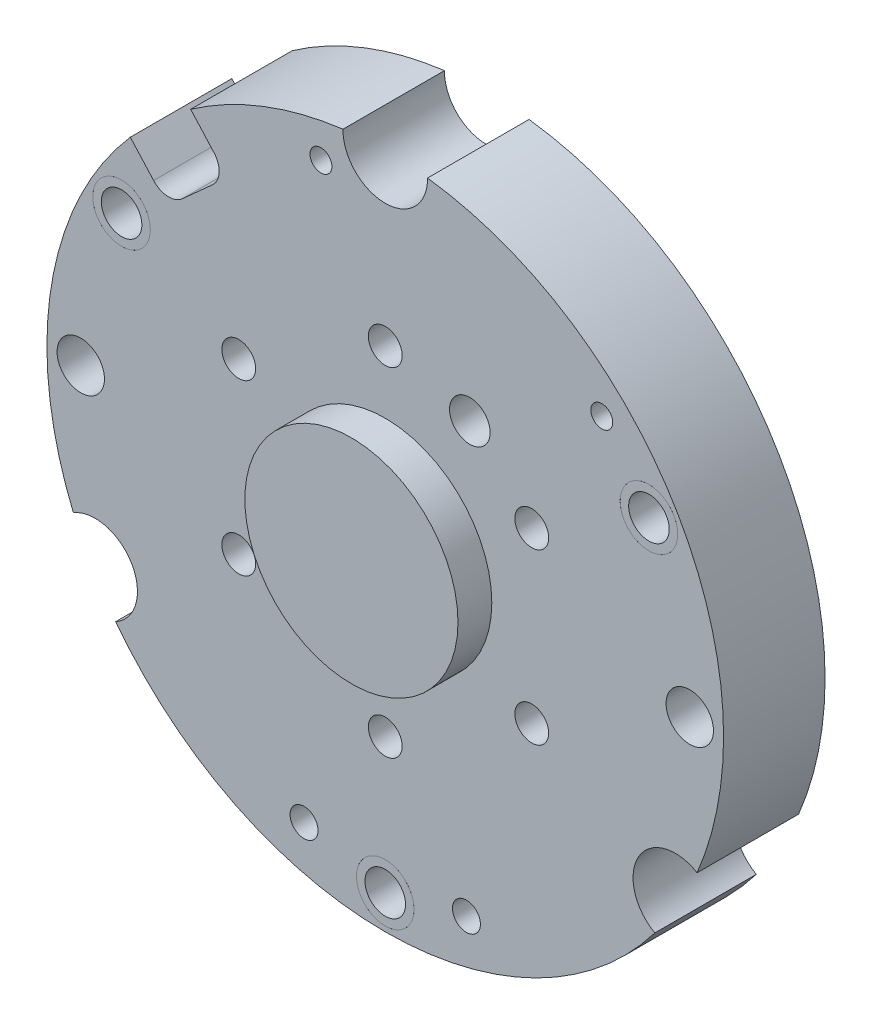
SolidWorks part; units mm, degrees
material "1060-H18"
ref_plane "Piano frontale" through (0, 0, 0) normal (0, 0, 1) x (1, 0, 0)
ref_plane "Piano superiore" through (0, 0, 0) normal (0, 1, 0) x (1, 0, 0)
ref_plane "Piano destro" through (0, 0, 0) normal (1, 0, 0) x (0, 0, -1)
sketch "Schizzo1" plane through (0, 0, 0) normal (0, 0, 1) x (1, 0, 0)
  line L3 (-34.2352, 29.0552) -> (-37.6736, 32.874)
  line L4 (-28.7559, 40.9035) -> (-25.3174, 37.0847)
  line L5 (-25.5395, 32.8479) -> (-29.9984, 28.8331)
  line L6 (-34.2352, 29.0552) -> (-37.6736, 32.874)
  line L7 (-28.7559, 40.9035) -> (-25.3174, 37.0847)
  line L8 (-25.5395, 32.8479) -> (-29.9984, 28.8331)
  arc A2 (32, 30.379) -> (32, 33.621) centre (32, 32) ccw
  arc A3 (32, 33.621) -> (32, 30.379) centre (32, 32) ccw
  arc A4 (32, 30.379) -> (32, 33.621) centre (32, 32) ccw
  arc A5 (32, 33.621) -> (32, 30.379) centre (32, 32) ccw
  arc A6 (-12, -44.067) -> (-12, -39.933) centre (-12, -42) ccw
  arc A7 (-12, -39.933) -> (-12, -44.067) centre (-12, -42) ccw
  arc A8 (-12, -44.067) -> (-12, -39.933) centre (-12, -42) ccw
  arc A9 (-34.2352, 29.0552) -> (-29.9984, 28.8331) centre (-32.0057, 31.0626) ccw
  arc A10 (-37.6736, 32.874) -> (-46.0866, -19.3913) centre (0, 0) ccw
  arc A11 (-39.8377, -30.2151) -> (-46.0866, -19.3913) centre (-42.87, -24.75) ccw
  arc A12 (-39.8377, -30.2151) -> (39.8377, -30.2151) centre (0, 0) ccw
  arc A13 (46.0866, -19.3913) -> (39.8377, -30.2151) centre (42.87, -24.75) ccw
  arc A14 (46.0866, -19.3913) -> (6.2491, 49.608) centre (0, 0) ccw
  arc A15 (-6.2491, 49.608) -> (6.2491, 49.608) centre (0, 49.5) ccw
  arc A16 (-6.2491, 49.608) -> (-28.7559, 40.9035) centre (0, 0) ccw
  arc A17 (-25.5395, 32.8479) -> (-25.3174, 37.0847) centre (-27.5469, 35.0773) ccw
  arc A18 (-34.2352, 29.0552) -> (-29.9984, 28.8331) centre (-32.0057, 31.0626) ccw
  arc A19 (-37.6736, 32.874) -> (-46.0866, -19.3913) centre (0, 0) ccw
  arc A20 (-39.8377, -30.2151) -> (-46.0866, -19.3913) centre (-42.87, -24.75) ccw
  arc A21 (-39.8377, -30.2151) -> (39.8377, -30.2151) centre (0, 0) ccw
  arc A22 (46.0866, -19.3913) -> (39.8377, -30.2151) centre (42.87, -24.75) ccw
  arc A23 (46.0866, -19.3913) -> (6.2491, 49.608) centre (0, 0) ccw
  arc A24 (-6.2491, 49.608) -> (6.2491, 49.608) centre (0, 49.5) ccw
  arc A25 (-6.2491, 49.608) -> (-28.7559, 40.9035) centre (0, 0) ccw
  arc A26 (-25.5395, 32.8479) -> (-25.3174, 37.0847) centre (-27.5469, 35.0773) ccw
  arc A27 (-12, -39.933) -> (-12, -44.067) centre (-12, -42) ccw
  arc A28 (12, -44.067) -> (12, -39.933) centre (12, -42) ccw
  arc A29 (12, -39.933) -> (12, -44.067) centre (12, -42) ccw
  arc A30 (12, -44.067) -> (12, -39.933) centre (12, -42) ccw
  arc A31 (12, -39.933) -> (12, -44.067) centre (12, -42) ccw
  arc A32 (-38.97, 26.75) -> (-38.97, 18.25) centre (-38.97, 22.5) ccw
  arc A33 (-38.97, 18.25) -> (-38.97, 26.75) centre (-38.97, 22.5) ccw
  arc A34 (-38.97, 26.75) -> (-38.97, 18.25) centre (-38.97, 22.5) ccw
  arc A35 (-38.97, 18.25) -> (-38.97, 26.75) centre (-38.97, 22.5) ccw
  arc A36 (38.97, 26.75) -> (38.97, 18.25) centre (38.97, 22.5) ccw
  arc A37 (38.97, 18.25) -> (38.97, 26.75) centre (38.97, 22.5) ccw
  arc A38 (38.97, 26.75) -> (38.97, 18.25) centre (38.97, 22.5) ccw
  arc A39 (38.97, 18.25) -> (38.97, 26.75) centre (38.97, 22.5) ccw
  arc A40 (0, -40.75) -> (0, -49.25) centre (0, -45) ccw
  arc A41 (0, -49.25) -> (0, -40.75) centre (0, -45) ccw
  arc A42 (0, -40.75) -> (0, -49.25) centre (0, -45) ccw
  arc A43 (0, -49.25) -> (0, -40.75) centre (0, -45) ccw
  arc A44 (-45, -3.5) -> (-45, 3.5) centre (-45, 0) ccw
  arc A45 (-45, 3.5) -> (-45, -3.5) centre (-45, 0) ccw
  arc A46 (-45, -3.5) -> (-45, 3.5) centre (-45, 0) ccw
  arc A47 (-45, 3.5) -> (-45, -3.5) centre (-45, 0) ccw
  arc A48 (45, -3.5) -> (45, 3.5) centre (45, 0) ccw
  arc A49 (45, 3.5) -> (45, -3.5) centre (45, 0) ccw
  arc A50 (45, -3.5) -> (45, 3.5) centre (45, 0) ccw
  arc A51 (45, 3.5) -> (45, -3.5) centre (45, 0) ccw
  arc A56 (-9.5, 42.379) -> (-9.5, 45.621) centre (-9.5, 44) ccw
  arc A57 (-9.5, 45.621) -> (-9.5, 42.379) centre (-9.5, 44) ccw
  arc A58 (-9.5, 42.379) -> (-9.5, 45.621) centre (-9.5, 44) ccw
  arc A59 (-9.5, 45.621) -> (-9.5, 42.379) centre (-9.5, 44) ccw
  dimension "D1" = 0
  dimension "D2" = 0
  dimension "D3" = 0
  dimension "D4" = 0
  dimension "D5" = 0
  dimension "D6" = 0
  dimension "D7" = 0
  dimension "D8" = 0
  dimension "D9" = 0
  dimension "D11" = 0
extrude "Estrusione-Estrusione1" add sketch "Schizzo1" along normal blind 15
sketch "Schizzo2" plane through (0, 0, 15) normal (0, 0, 1) x (1, 0, 0)
  arc A2 (-2.1651, -23.75) -> (2.1651, -26.25) centre (0, -25) ccw
  arc A3 (2.1651, -26.25) -> (-2.1651, -23.75) centre (0, -25) ccw
  arc A4 (-2.1651, -23.75) -> (2.1651, -26.25) centre (0, -25) ccw
  arc A5 (2.1651, -26.25) -> (-2.1651, -23.75) centre (0, -25) ccw
  arc A6 (19.4856, -11.25) -> (23.8157, -13.75) centre (21.6506, -12.5) ccw
  arc A7 (23.8157, -13.75) -> (19.4856, -11.25) centre (21.6506, -12.5) ccw
  arc A8 (19.4856, -11.25) -> (23.8157, -13.75) centre (21.6506, -12.5) ccw
  arc A9 (23.8157, -13.75) -> (19.4856, -11.25) centre (21.6506, -12.5) ccw
  arc A10 (19.4856, 13.75) -> (23.8157, 11.25) centre (21.6506, 12.5) ccw
  arc A11 (23.8157, 11.25) -> (19.4856, 13.75) centre (21.6506, 12.5) ccw
  arc A12 (19.4856, 13.75) -> (23.8157, 11.25) centre (21.6506, 12.5) ccw
  arc A13 (23.8157, 11.25) -> (19.4856, 13.75) centre (21.6506, 12.5) ccw
  arc A14 (9.9019, 23.1506) -> (15.0981, 20.1506) centre (12.5, 21.6506) ccw
  arc A15 (15.0981, 20.1506) -> (9.9019, 23.1506) centre (12.5, 21.6506) ccw
  arc A16 (9.9019, 23.1506) -> (15.0981, 20.1506) centre (12.5, 21.6506) ccw
  arc A17 (15.0981, 20.1506) -> (9.9019, 23.1506) centre (12.5, 21.6506) ccw
  arc A22 (-23.8157, -11.25) -> (-19.4856, -13.75) centre (-21.6506, -12.5) ccw
  arc A23 (-19.4856, -13.75) -> (-23.8157, -11.25) centre (-21.6506, -12.5) ccw
  arc A24 (-23.8157, -11.25) -> (-19.4856, -13.75) centre (-21.6506, -12.5) ccw
  arc A25 (-19.4856, -13.75) -> (-23.8157, -11.25) centre (-21.6506, -12.5) ccw
  arc A26 (-2.1651, 26.25) -> (2.1651, 23.75) centre (0, 25) ccw
  arc A27 (2.1651, 23.75) -> (-2.1651, 26.25) centre (0, 25) ccw
  arc A28 (-2.1651, 26.25) -> (2.1651, 23.75) centre (0, 25) ccw
  arc A29 (2.1651, 23.75) -> (-2.1651, 26.25) centre (0, 25) ccw
  arc A30 (-23.8157, 13.75) -> (-19.4856, 11.25) centre (-21.6506, 12.5) ccw
  arc A31 (-19.4856, 11.25) -> (-23.8157, 13.75) centre (-21.6506, 12.5) ccw
  arc A32 (-23.8157, 13.75) -> (-19.4856, 11.25) centre (-21.6506, 12.5) ccw
  arc A33 (-19.4856, 11.25) -> (-23.8157, 13.75) centre (-21.6506, 12.5) ccw
  dimension "D1" = 0
  dimension "D2" = 0
  dimension "D3" = 0
  dimension "D4" = 0
  dimension "D6" = 0
  dimension "D7" = 0
  dimension "D8" = 0
extrude "Taglio-Estrusione1" cut sketch "Schizzo2" against normal blind 15
sketch "Schizzo3" plane through (0, 0, 0) normal (0, 0, -1) x (-1, 0, 0)
  circle A74 centre (0, 25) radius 5.5
  circle A75 centre (0, 25) radius 5.5
  circle A85 centre (21.6506, 12.5) radius 5.5
  circle A86 centre (21.6506, -12.5) radius 5.5
  circle A87 centre (0, -25) radius 5.5
  circle A88 centre (-21.6506, -12.5) radius 5.5
  circle A89 centre (-21.6506, 12.5) radius 5.5
  dimension "D1" = 3
extrude "Taglio-Estrusione2" cut sketch "Schizzo3" against normal blind 5
sketch "Schizzo5" plane through (0, 0, 15) normal (0, 0, 1) x (1, 0, 0)
  arc A2 (13.6399, -7.875) -> (-13.6399, 7.875) centre (0, 0) ccw
  arc A3 (-13.6399, 7.875) -> (13.6399, -7.875) centre (0, 0) ccw
  arc A6 (13.6399, -7.875) -> (-13.6399, 7.875) centre (0, 0) ccw
  arc A7 (-13.6399, 7.875) -> (13.6399, -7.875) centre (0, 0) ccw
  dimension "D1" = 0
extrude "Estrusione-Estrusione2" add sketch "Schizzo5" along normal blind 5 separate body contours A7 A6
sketch "Schizzo6" plane through (0, 0, 0) normal (0, 0, -1) x (-1, 0, 0)
  circle A0 centre (0, 0) radius 35
extrude "Taglio-Estrusione3" cut sketch "Schizzo6" against normal blind 0.3
sketch "Schizzo7" plane through (0, 0, 0) normal (0, 0, -1) x (-1, 0, 0)
  circle A0 centre (38.97, 22.5) radius 3
  circle A1 centre (0, -44.998) radius 3
  circle A2 centre (-38.97, 22.5) radius 3
  circle A3 centre (38.97, 22.5) radius 4.25 construction
  circle A4 centre (0, -45) radius 4.25 construction
  circle A5 centre (-38.97, 22.5) radius 4.25 construction
  circle A6 centre (38.97, 22.5) radius 4.25
  circle A7 centre (0, -45) radius 4.25
  circle A8 centre (-38.97, 22.5) radius 4.25
  point P10 (0, 0.0007)
  point P17 (0, 0)
  dimension "D1" = 6
  dimension "D2" = 3
extrude "Estrusione-Estrusione3" add sketch "Schizzo7" against normal blind 15 separate body
